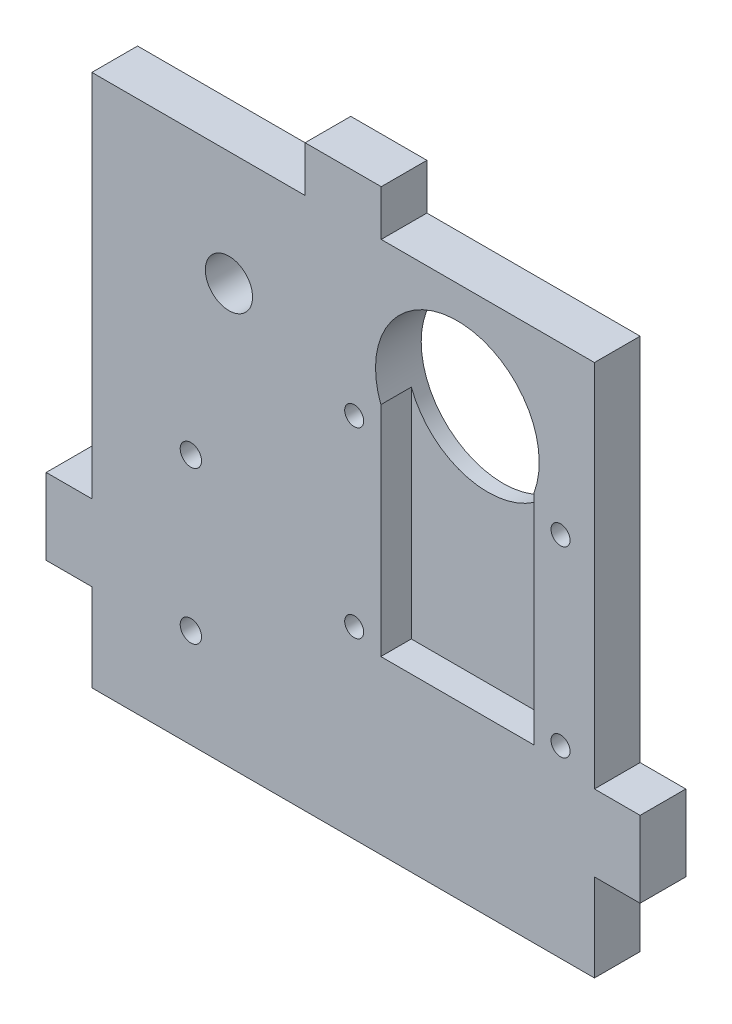
SolidWorks part; units mm, degrees
ref_plane "Plan de face" through (0, 0, 0) normal (0, 0, 1) x (1, 0, 0)
ref_plane "Plan de dessus" through (0, 0, 0) normal (0, 1, 0) x (1, 0, 0)
ref_plane "Plan de droite" through (0, 0, 0) normal (1, 0, 0) x (0, 0, -1)
sketch "Esquisse1" plane through (0, 0, 0) normal (0, 0, 1) x (1, 0, 0)
  line L0 (-15, 0) -> (15, 0)
  line L1 (0, 34.4414) -> (0, -34.4414) construction
  line L2 (33, 15) -> (-33, 15)
  line L3 (-33, 15) -> (-33, -55)
  line L4 (-33, -55) -> (33, -55)
  line L5 (33, 15) -> (33, -55)
  circle A1 centre (15, 0) radius 10.75
  circle A4 centre (-20, -42) radius 1.4
  circle A5 centre (-20, -22) radius 1.4
  circle A6 centre (-15, 0) radius 3.1
  point P3 (0, 0)
  point P14 (0, 15)
  point P15 (-15, 0)
  point P16 (15, 0)
  dimension "D5" = 6.2
  dimension "D7" = 2.8
  dimension "D8" = 2.8
  dimension "D10" = 13
  dimension "D11" = 13
  dimension "D13" = 21.5
  dimension "D1" = 15
  dimension "D2" = 33
  dimension "D3" = 70
  dimension "D4" = 15
  dimension "D6" = 66
  dimension "D9" = 13
  dimension "D12" = 20
extrude "Boss.-Extru.1" add sketch "Esquisse1" along normal blind 6
sketch "Esquisse2" plane through (0, 0, 6) normal (0, 0, 1) x (1, 0, 0)
  line L1 (33, 15) -> (-33, 15) construction
  line L2 (-5, 15) -> (5, 15)
  line L3 (-5, 15) -> (-5, 21)
  line L4 (-5, 21) -> (5, 21)
  line L7 (5, 15) -> (5, 21)
  line L8 (-33, 15) -> (-33, -55) construction
  line L9 (33, 15) -> (33, -55) construction
  line L10 (-33, -33.5) -> (-39, -33.5)
  line L11 (-33, -33.5) -> (-33, -43.5)
  line L12 (-33, -43.5) -> (-39, -43.5)
  line L13 (-39, -33.5) -> (-39, -43.5)
  line L14 (33, -33.5) -> (39, -33.5)
  line L15 (33, -33.5) -> (33, -43.5)
  line L16 (33, -43.5) -> (39, -43.5)
  line L17 (39, -33.5) -> (39, -43.5)
  line L18 (-33, -55) -> (33, -55) construction
  dimension "D1" = 28
  dimension "D2" = 10
  dimension "D3" = 6
  dimension "D4" = 6
  dimension "D5" = 10
  dimension "D6" = 11.5
  dimension "D7" = 11.5
  dimension "D8" = 10
  dimension "D9" = 6
extrude "Boss.-Extru.3" add sketch "Esquisse2" against normal blind 6
sketch "Esquisse3" plane through (0, 0, 6) normal (0, 0, 1) x (1, 0, 0)
  line L0 (4.95, -3.8158) -> (4.95, -32.4658)
  line L1 (4.95, -32.4658) -> (25.05, -32.4658)
  line L2 (25.05, -32.4658) -> (25.05, -3.8158)
  circle A0 centre (15, 0) radius 10.75 construction
  arc A1 (4.95, -3.8158) -> (25.05, -3.8158) centre (15, 0) ccw
  dimension "D1" = 28.65
  dimension "D2" = 20.1
  dimension "D3" = 28.65
extrude "Enlèv. mat.-Extru.3" cut sketch "Esquisse3" against normal blind 4
sketch "Esquisse4" plane through (0, 0, 6) normal (0, 0, 1) x (1, 0, 0)
  line L0 (4.95, -3.8158) -> (4.95, -32.4658) construction
  line L1 (25.05, -32.4658) -> (25.05, -3.8158) construction
  line L3 (4.95, -32.4658) -> (25.05, -32.4658) construction
  circle A0 centre (28.55, -6.8158) radius 1.25
  circle A2 centre (28.55, -30.8158) radius 1.25
  circle A4 centre (1.45, -30.8158) radius 1.25
  circle A6 centre (1.45, -6.8158) radius 1.25
  dimension "D1" = 2.5
  dimension "D2" = 2.5
  dimension "D3" = 2.5
  dimension "D4" = 2.5
  dimension "D5" = 24
  dimension "D6" = 24
  dimension "D7" = 3.5
  dimension "D8" = 3.5
  dimension "D9" = 3.5
  dimension "D10" = 3.5
  dimension "D11" = 1.65
  dimension "D12" = 1.65
extrude "Enlèv. mat.-Extru.4" cut sketch "Esquisse4" against normal blind 6
